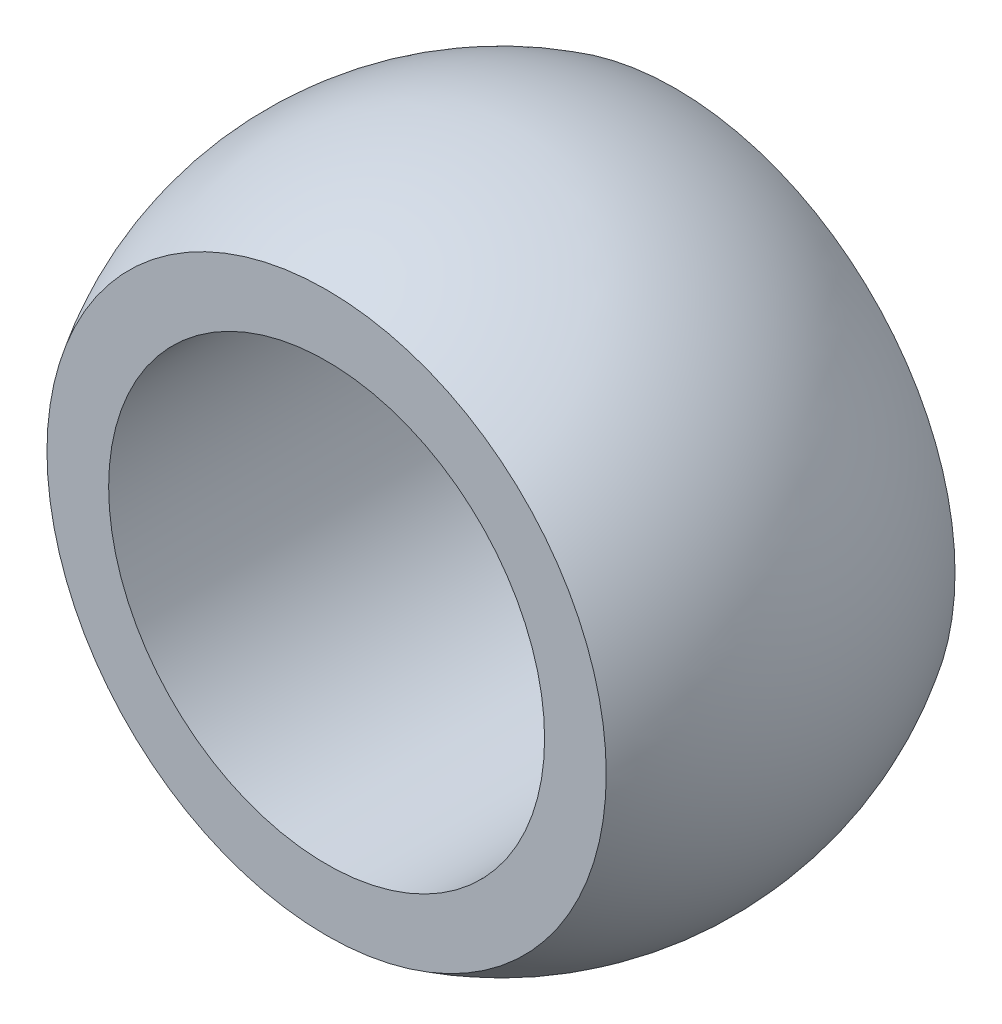
SolidWorks part; units mm, degrees
ref_plane "Front Plane" through (0, 0, 0) normal (0, 0, 1) x (1, 0, 0)
ref_plane "Top Plane" through (0, 0, 0) normal (0, 1, 0) x (1, 0, 0)
ref_plane "Right Plane" through (0, 0, 0) normal (1, 0, 0) x (0, 0, -1)
sketch "Sketch1" plane through (0, 0, 0) normal (0, 1, 0) x (1, 0, 0)
  line L0 (0, 16.516) -> (0, -16.516) construction
  line L1 (0, 12.0002) -> (0, -12.0002)
  arc A0 (0, -12.0002) -> (0, 12.0002) centre (0, 0) ccw
  dimension "D1" = 24.0005
revolve "Revolve1" add sketch "Sketch1" angle 360 about L0
sketch "Sketch2" plane through (0, 0, 0) normal (1, 0, 0) x (0, 0, -1)
  line L0 (0, 12.0002) -> (0, -12.0002) construction
  line L1 (-6.35, 10.1825) -> (-6.35, -10.1825)
  line L2 (6.35, 10.1825) -> (6.35, -10.1825)
  circle A0 centre (0, 0) radius 12.0002 construction
  arc A1 (0, -12.0002) -> (6.35, 10.1825) centre (0, 0) ccw
  arc A2 (-6.35, 10.1825) -> (-6.35, -10.1825) centre (0, 0) ccw
  dimension "D1" = 12.7
extrude "Cut-Extrude1" cut sketch "Sketch2" against normal through all both and the other way through all contours L1 A2 | L2 A1
sketch "Sketch3" plane through (0, 0, 6.35) normal (0, 0, 1) x (1, 0, 0)
  circle A0 centre (0, 0) radius 7.9375
  dimension "D1" = 15.875
extrude "Cut-Extrude3" cut sketch "Sketch3" against normal through all
